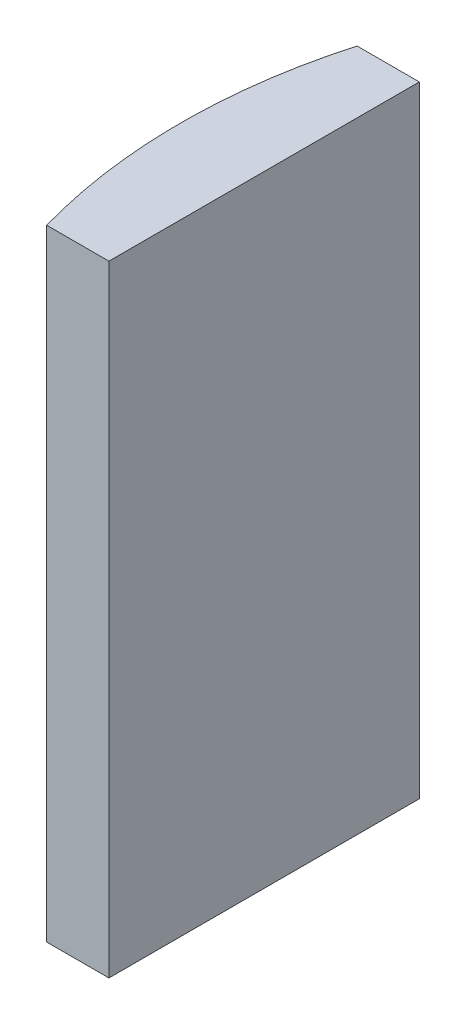
SolidWorks part; units mm, degrees
ref_plane "前视基准面" through (0, 0, 0) normal (0, 0, 1) x (1, 0, 0)
ref_plane "上视基准面" through (0, 0, 0) normal (0, 1, 0) x (1, 0, 0)
ref_plane "右视基准面" through (0, 0, 0) normal (1, 0, 0) x (0, 0, -1)
sketch "草图1" plane through (0, 0, 0) normal (0, 1, 0) x (1, 0, 0)
  line L0 (-137.6835, 0) -> (10.8051, 0) construction
  line L1 (-13.2693, 5) -> (-11.2648, 5)
  line L2 (-13.2693, -5) -> (-11.2648, -5)
  line L3 (-11.2648, 5) -> (-11.2648, -5)
  arc A0 (-13.2693, 5) -> (-13.2693, -5) centre (4.3552, 0) ccw
  point P2 (-13.9648, 0)
  point P4 (-11.2648, 0)
  dimension "D2" = 5
  dimension "D3" = 18.32
  dimension "D4" = 2.7
  dimension "D1" = 5
extrude "凸台-拉伸1" add sketch "草图1" along normal blind 20
